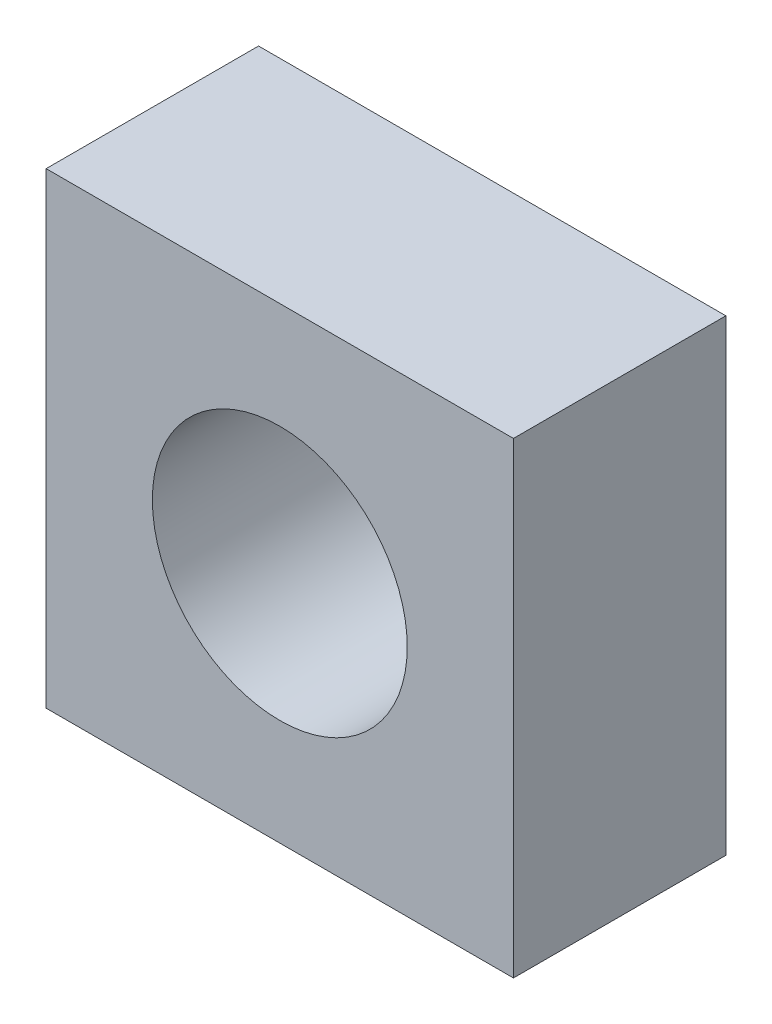
SolidWorks part; units mm, degrees
ref_plane "Front Plane" through (0, 0, 0) normal (0, 0, 1) x (1, 0, 0)
ref_plane "Top Plane" through (0, 0, 0) normal (0, 1, 0) x (1, 0, 0)
ref_plane "Right Plane" through (0, 0, 0) normal (1, 0, 0) x (0, 0, -1)
sketch "Sketch1" plane through (0, 0, 0) normal (0, 0, 1) x (1, 0, 0)
  line L1 (-2.75, -2.75) -> (2.75, -2.75)
  line L2 (-2.75, -2.75) -> (-2.75, 2.75)
  line L3 (-2.75, 2.75) -> (2.75, 2.75)
  line L4 (2.75, -2.75) -> (2.75, 2.75)
  line L5 (-2.75, -2.75) -> (2.75, 2.75) construction
  line L6 (-2.75, 2.75) -> (2.75, -2.75) construction
  circle A0 centre (0, 0) radius 1.5
  point P0 (0, 0)
  dimension "D2" = 3
  dimension "D1" = 5.5
extrude "Boss-Extrude1" add sketch "Sketch1" along normal blind 2.5
